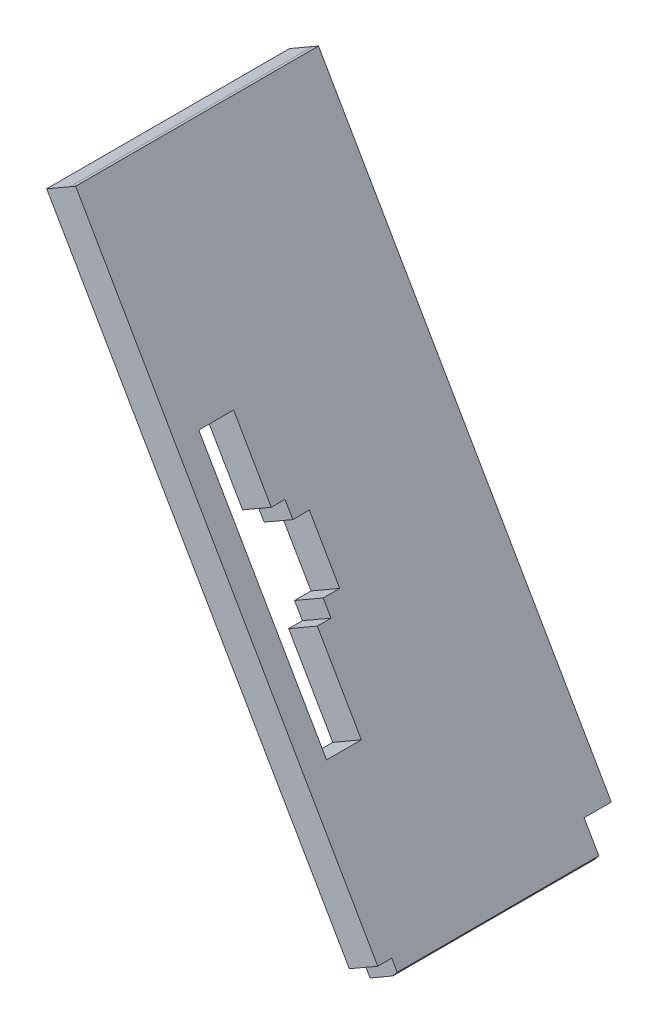
SolidWorks part; units mm, degrees
ref_plane "Alzado" through (0, 0, 0) normal (0, 0, 1) x (1, 0, 0)
ref_plane "Planta" through (0, 0, 0) normal (0, 1, 0) x (1, 0, 0)
ref_plane "Vista lateral" through (0, 0, 0) normal (1, 0, 0) x (0, 0, -1)
sketch "Croquis1" plane through (0, 0, 0) normal (0, 0, 1) x (1, 0, 0)
  line L0 (-99.8897, -0.0106) -> (-102.3678, -1.4414)
  line L1 (-51.6, -89.3738) -> (-103.2, 0) construction
  line L2 (-102.3678, -1.4414) -> (-103.4327, -2.0562)
  line L3 (-99.8167, -8.3193) -> (-104.6188, -0.0017) construction
  line L4 (-103.4327, -2.0562) -> (-56.2941, -83.7025)
  line L5 (-52.8293, -81.7021) -> (-56.3777, -83.7508) construction
  line L6 (-56.2941, -83.7025) -> (-52.8293, -81.7021)
  line L7 (-52.8293, -81.7021) -> (-99.8897, -0.0106) construction
  line L8 (-99.8897, -0.0106) -> (-99.0232, 0.4885)
  line L9 (-99.0232, 0.4885) -> (-52.1531, -80.8725)
  line L10 (-52.1531, -80.8725) -> (-52.8293, -81.7021)
  dimension "D1" = 1
extrude "Saliente-Extruir1" add sketch "Croquis1" along normal up to surface (123.1433 mm away)
sketch "Croquis2" plane through (-78.4648, -45.3017, 0) normal (-0.866, -0.5, 0) x (0, 0, 1)
  line L0 (4.1425, -44.3415) -> (4.1425, -39.4594)
  line L1 (35, -44.3415) -> (4, -44.3415) construction
  line L2 (4.1425, -39.4594) -> (0, -39.4594)
  line L3 (0, 49.9356) -> (0, -44.3415) construction
  line L4 (34.8637, -44.3415) -> (34.8637, -42.2926)
  line L5 (37, -44.3415) -> (0, -44.3415) construction
  line L6 (34.8637, -42.2926) -> (37, -42.2926)
  line L7 (37, -44.3415) -> (37, 49.9356) construction
  line L8 (34.8637, -44.3415) -> (34.8637, -44.9848)
  line L9 (34.8637, -44.9848) -> (37.496, -44.9848)
  line L10 (37.496, -44.9848) -> (37.496, -42.2926)
  line L11 (37.496, -42.2926) -> (37, -42.2926)
  line L12 (4.1425, -44.3415) -> (4.1425, -44.6631)
  line L13 (4.1425, -44.6631) -> (-0.1146, -44.6631)
  line L14 (-0.1146, -44.6631) -> (-0.1146, -39.4594)
  line L15 (-0.1146, -39.4594) -> (0, -39.4594)
extrude "Cortar-Extruir1" cut sketch "Croquis2" against normal blind 11
sketch "Croquis3" plane through (-78.4648, -45.3017, 0) normal (-0.866, -0.5, 0) x (0, 0, 1)
  line L8 (0, 49.9356) -> (0, -39.4594)
  line L9 (0, -39.4594) -> (4.1425, -39.4594)
  line L10 (4.1425, -39.4594) -> (4.1425, -44.3415)
  line L11 (4.1425, -44.3415) -> (34.8637, -44.3415)
  line L12 (34.8637, -44.3415) -> (34.8637, -42.2926)
  line L13 (34.8637, -42.2926) -> (37, -42.2926)
  line L14 (37, -42.2926) -> (37, 49.9356)
  line L15 (37, 49.9356) -> (0, 49.9356)
  line L16 (0, 49.9356) -> (0, -39.4594)
  line L17 (0, -39.4594) -> (4.1425, -39.4594)
  line L18 (4.1425, -39.4594) -> (4.1425, -44.3415)
  line L19 (4.1425, -44.3415) -> (34.8637, -44.3415)
  line L20 (34.8637, -44.3415) -> (34.8637, -42.2926)
  line L21 (34.8637, -42.2926) -> (37, -42.2926)
  line L22 (37, -42.2926) -> (37, 49.9356)
  line L23 (37, 49.9356) -> (0, 49.9356)
  dimension "D1" = 0
sketch "Croquis4" plane through (-74.0958, -42.7826, 0) normal (-0.8665, -0.4992, 0) x (0, 0, 1)
  line L0 (33.2244, 0.0009) -> (33.4244, 0.0009)
  line L1 (33.2244, -14.9486) -> (33.2244, 14.9503) construction
  line L2 (33.4244, -19.4991) -> (33.4244, 19.5009)
  line L3 (33.4244, 19.5009) -> (28.1244, 19.5009)
  line L4 (28.1244, 19.5009) -> (28.1244, -19.4991)
  line L5 (33.4244, -19.4991) -> (28.1244, -19.4991)
  point P8 (28.1244, 0.0009)
extrude "Cortar-Extruir2" cut sketch "Croquis4" along normal blind 10
sketch "Croquis5" plane through (-74.0958, -42.7826, 0) normal (-0.8665, -0.4992, 0) x (0, 0, 1)
  line L0 (28.2244, 7.9916) -> (26.0346, 7.9916)
  line L1 (28.2244, -14.9486) -> (28.2244, 14.9503) construction
  line L2 (26.0346, 7.9916) -> (26.0346, 5.6022)
  line L3 (26.0346, 5.6022) -> (23.5161, 5.6022)
  line L4 (23.5161, 5.6022) -> (23.5161, -3.6589)
  line L6 (26.0346, -3.6589) -> (23.5161, -3.6589)
  line L7 (26.0346, -6.0482) -> (26.0346, -3.6589)
  line L8 (28.2244, -6.0482) -> (26.0346, -6.0482)
  line L9 (28.2244, 7.9916) -> (28.7264, 7.9916)
  line L10 (28.7264, 7.9916) -> (28.7264, -6.0482)
  line L11 (28.7264, -6.0482) -> (28.2244, -6.0482)
extrude "Cortar-Extruir3" cut sketch "Croquis5" along normal blind 7
